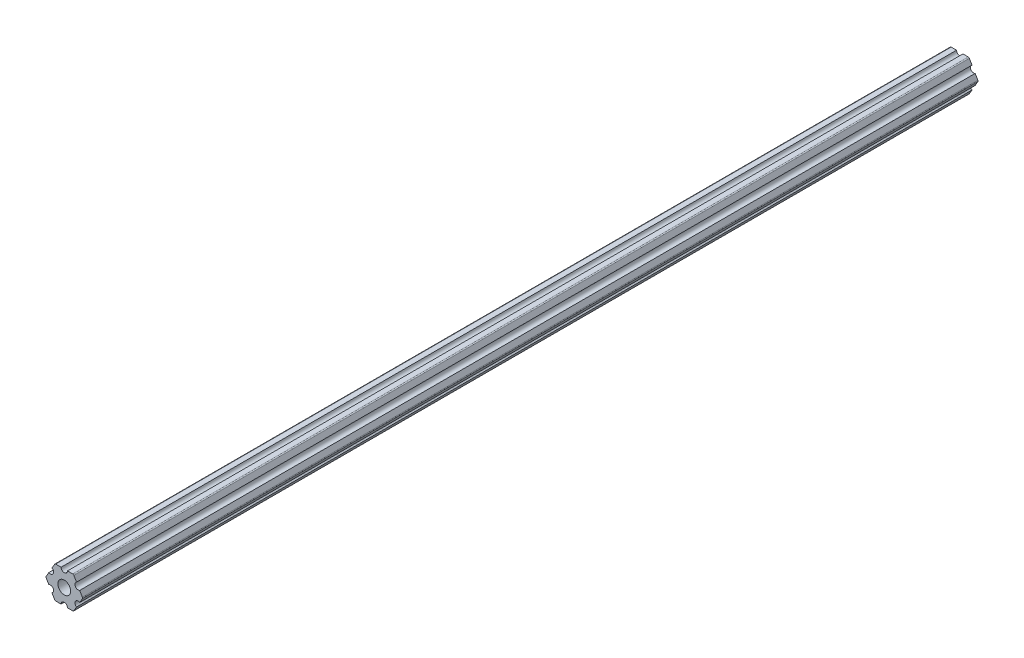
SolidWorks part; units mm, degrees
ref_plane "Front Plane" through (0, 0, 0) normal (0, 0, 1) x (1, 0, 0)
ref_plane "Top Plane" through (0, 0, 0) normal (0, 1, 0) x (1, 0, 0)
ref_plane "Right Plane" through (0, 0, 0) normal (1, 0, 0) x (0, 0, -1)
sketch "Sketch1" plane through (0, 0, 0) normal (0, 0, 1) x (1, 0, 0)
  line L1 (7.3323, 0) -> (3.6662, 6.35)
  line L2 (3.6662, 6.35) -> (-3.6662, 6.35)
  line L3 (-3.6662, 6.35) -> (-7.3323, 0)
  line L4 (-7.3323, 0) -> (-3.6662, -6.35)
  line L5 (-3.6662, -6.35) -> (3.6662, -6.35)
  line L6 (3.6662, -6.35) -> (7.3323, 0)
  circle A0 centre (0, 0) radius 6.35 construction
  dimension "D1" = 12.7
extrude "Boss-Extrude1" add sketch "Sketch1" along normal blind 355.6
sketch "Sketch2" plane through (0, 0, 355.6) normal (0, 0, 1) x (1, 0, 0)
  line L0 (3.6662, 6.35) -> (-3.6662, 6.35) construction
  line L1 (7.3323, 0) -> (3.6662, 6.35) construction
  line L2 (3.6662, -6.35) -> (7.3323, 0) construction
  line L3 (-3.6662, -6.35) -> (3.6662, -6.35) construction
  line L4 (-7.3323, 0) -> (-3.6662, -6.35) construction
  line L5 (-3.6662, 6.35) -> (-7.3323, 0) construction
  circle A0 centre (0, 6.35) radius 1.27
  circle A1 centre (5.4993, 3.175) radius 1.27
  circle A2 centre (5.4993, -3.175) radius 1.27
  circle A3 centre (0, -6.35) radius 1.27
  circle A4 centre (-5.4993, -3.175) radius 1.27
  circle A5 centre (-5.4993, 3.175) radius 1.27
  circle A6 centre (0, 0) radius 2.54
  dimension "D1" = 2.54
  dimension "D2" = 5.08
extrude "Cut-Extrude1" cut sketch "Sketch2" against normal through all
fillet "Fillet1" radius 0.508 6 edges at (-3.6662, 6.35, 177.8) (-7.3323, 0, 177.8) (-3.6662, -6.35, 177.8) (3.6662, -6.35, 177.8) (7.3323, 0, 177.8) (3.6662, 6.35, 177.8)
hole_wizard "1/4-20 Tapped Hole3" positions "Sketch5" profile "Sketch6" tap size "1/4-20" standard "ANSI Inch" end condition through all
sketch "Sketch5" plane through (0, 0, 355.6) normal (0, 0, 1) x (1, 0, 0)
  point P0 (0, 0)
sketch "Sketch6" plane through (0, 0, 355.6) normal (1, 0, 0) x (0, -1, 0)
  line L0 (0, 0) -> (0, 355.6)
  line L1 (0, 355.6) -> (2.5527, 355.6)
  line L2 (2.5527, 355.6) -> (2.5527, 0)
  line L5 (2.5527, 0) -> (0, 0)
  line L11 (0, -6.35) -> (0, 107.95) construction
  dimension "Thru Tap Drill Dia." = 5.1054
  dimension "Thru Tap Drill Depth" = 355.6
cosmetic thread "Hole Thread1" parameters "D1"=12.7, "D2"=6.35
ref_plane "Plane1" through (0, 0, 177.8) normal (0, 0, 1) x (1, 0, 0)
mirror "Mirror1" about plane through (0, 0, 177.8) normal (0, 0, 1) of "1/4-20 Tapped Hole3"
